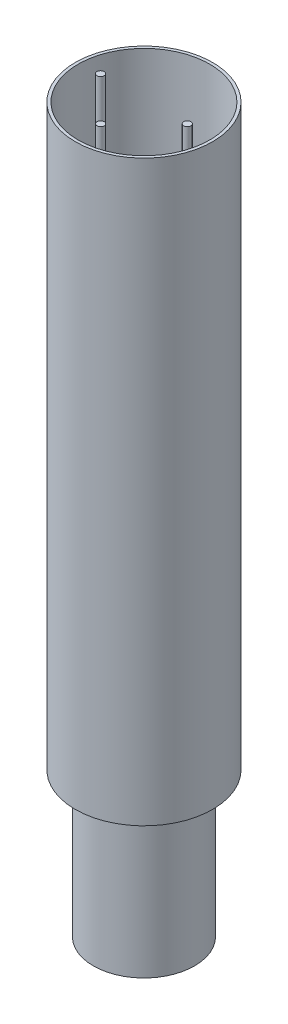
SolidWorks part; units mm, degrees
ref_plane "Front Plane" through (0, 0, 0) normal (0, 0, 1) x (1, 0, 0)
ref_plane "Top Plane" through (0, 0, 0) normal (0, 1, 0) x (1, 0, 0)
ref_plane "Right Plane" through (0, 0, 0) normal (1, 0, 0) x (0, 0, -1)
sketch "Sketch1" plane through (0, 0, 0) normal (0, 1, 0) x (1, 0, 0)
  circle A0 centre (0, 0) radius 35
  dimension "D1" = 70
extrude "Boss-Extrude1" add sketch "Sketch1" along normal blind 100
sketch "Sketch2" plane through (0, 100, 0) normal (0, 1, 0) x (1, 0, 0)
  circle A0 centre (0, 0) radius 47.5
  dimension "D1" = 95
extrude "Boss-Extrude2" add sketch "Sketch2" along normal blind 400
shell "Shell1" thickness 2
sketch "Sketch3" plane through (0, 102, 0) normal (0, 1, 0) x (1, 0, 0)
  circle A3 centre (0, -30) radius 2.5
  circle A7 centre (0, 0) radius 30 construction
  circle A10 centre (-30, 0) radius 2.5
  circle A11 centre (30, 0) radius 2.5
  dimension "D1" = 60
  dimension "D2" = 5
  dimension "D4" = 90
  dimension "D3" = 5
  dimension "D5" = 90
extrude "Boss-Extrude3" add sketch "Sketch3" along normal blind 400
